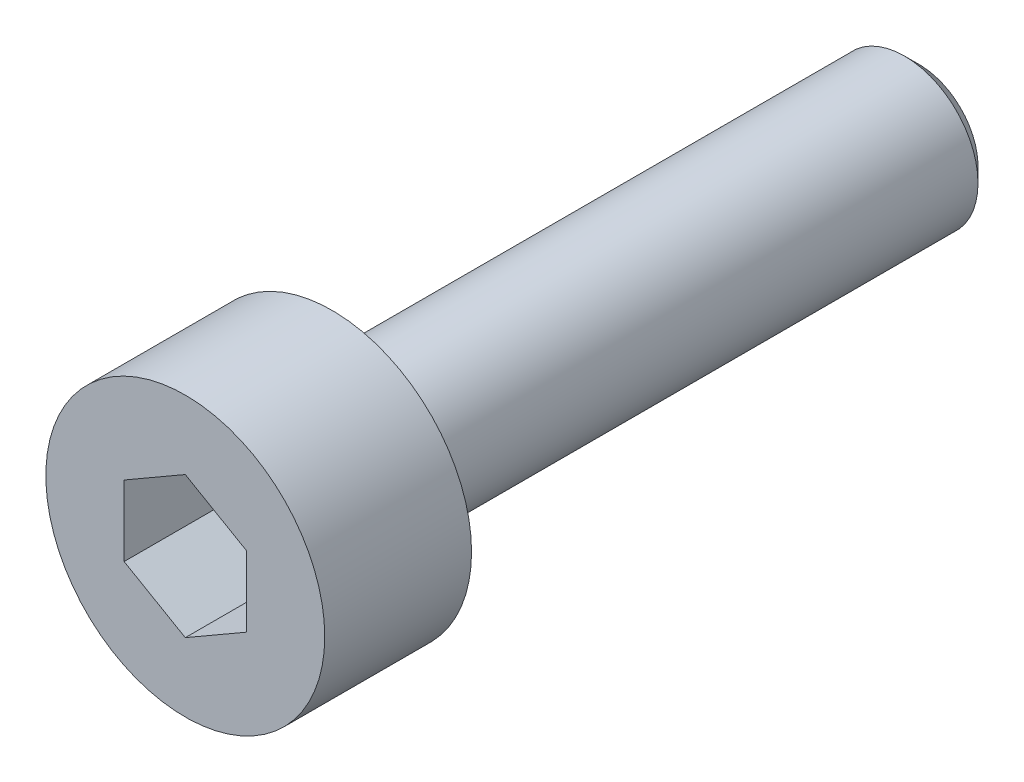
SolidWorks part; units mm, degrees
ref_plane "Front Plane" through (0, 0, 0) normal (0, 0, 1) x (1, 0, 0)
ref_plane "Top Plane" through (0, 0, 0) normal (0, 1, 0) x (1, 0, 0)
ref_plane "Right Plane" through (0, 0, 0) normal (1, 0, 0) x (0, 0, -1)
sketch "Sketch1" plane through (0, 0, 0) normal (0, 0, 1) x (1, 0, 0)
  circle A0 centre (0, 0) radius 2.85
  dimension "D1" = 5.7
extrude "Boss-Extrude1" add sketch "Sketch1" along normal blind 3
sketch "Sketch2" plane through (0, 0, 0) normal (0, 0, -1) x (-1, 0, 0)
  circle A0 centre (0, 0) radius 1.5
  dimension "D1" = 3
extrude "Boss-Extrude2" add sketch "Sketch2" along normal blind 12
chamfer "Chamfer1" distance 0.3 angle 45 1 edges at (-1.5, 0, -12)
sketch "Sketch3" plane through (0, 0, 3) normal (0, 0, 1) x (1, 0, 0)
  line L1 (0, 1.4434) -> (-1.25, 0.7217)
  line L2 (-1.25, 0.7217) -> (-1.25, -0.7217)
  line L3 (-1.25, -0.7217) -> (0, -1.4434)
  line L4 (0, -1.4434) -> (1.25, -0.7217)
  line L5 (1.25, -0.7217) -> (1.25, 0.7217)
  line L6 (1.25, 0.7217) -> (0, 1.4434)
  circle A0 centre (0, 0) radius 1.25 construction
  dimension "D1" = 2.5
extrude "Cut-Extrude1" cut sketch "Sketch3" against normal blind 2
